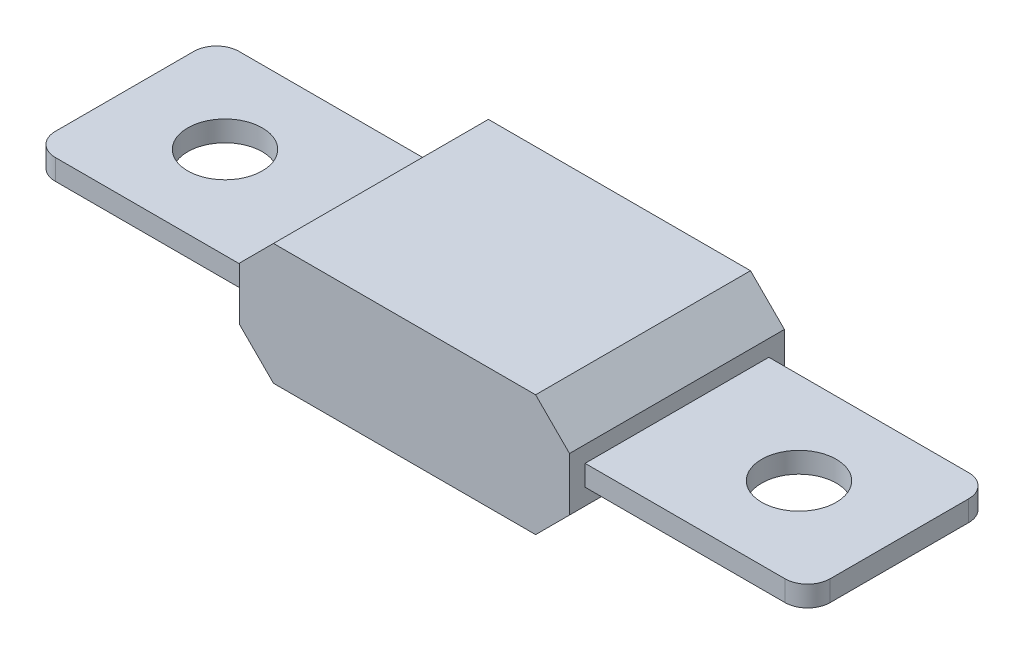
SolidWorks part; units mm, degrees
ref_plane "Front Plane" through (0, 0, 0) normal (0, 0, 1) x (1, 0, 0)
ref_plane "Top Plane" through (0, 0, 0) normal (0, 1, 0) x (1, 0, 0)
ref_plane "Right Plane" through (0, 0, 0) normal (1, 0, 0) x (0, 0, -1)
sketch "Sketch1" plane through (0, 0, 0) normal (0, 1, 0) x (1, 0, 0)
  line L0 (0, -8.13) -> (0, 8.13) construction
  line L1 (-32.29, 8.13) -> (32.29, 8.13)
  line L2 (-34.29, 6.13) -> (-34.29, -6.13)
  line L3 (-32.29, -8.13) -> (32.29, -8.13)
  line L4 (34.29, 6.13) -> (34.29, -6.13)
  line L5 (-34.29, 8.13) -> (34.29, -8.13) construction
  line L6 (-34.29, -8.13) -> (34.29, 8.13) construction
  circle A0 centre (25.4, 0) radius 3.3
  arc A1 (-32.29, 8.13) -> (-34.29, 6.13) centre (-32.29, 6.13) ccw
  arc A2 (-34.29, -6.13) -> (-32.29, -8.13) centre (-32.29, -6.13) ccw
  arc A3 (32.29, 8.13) -> (34.29, 6.13) centre (32.29, 6.13) cw
  arc A4 (32.29, -8.13) -> (34.29, -6.13) centre (32.29, -6.13) ccw
  circle A5 centre (-25.4, 0) radius 3.3
  point P0 (0, 0)
  dimension "D3" = 25.4
  dimension "D4" = 6.6
  dimension "D5" = 2
  dimension "D1" = 68.58
  dimension "D2" = 16.26
extrude "Boss-Extrude1" add sketch "Sketch1" along normal blind 1.83
sketch "Sketch2" plane through (0, 0, 0) normal (0, 0, 1) x (1, 0, 0)
  line L0 (-14.6, 3.275) -> (-11.6, 6.275)
  line L1 (-11.6, 6.275) -> (11.6, 6.275)
  line L2 (-14.6, 3.275) -> (-14.6, -1.445)
  line L3 (-11.6, -4.445) -> (11.6, -4.445)
  line L4 (14.6, 3.275) -> (14.6, -1.445)
  line L5 (-14.6, 6.275) -> (14.6, -4.445) construction
  line L6 (-14.6, -4.445) -> (14.6, 6.275) construction
  line L7 (-14.6, -1.445) -> (-11.6, -4.445)
  line L8 (11.6, 6.275) -> (14.6, 3.275)
  line L9 (11.6, -4.445) -> (14.6, -1.445)
  point P0 (0, 0.915)
  dimension "D1" = 29.2
  dimension "D2" = 0
  dimension "D3" = 10.72
extrude "Boss-Extrude2" add sketch "Sketch2" along normal blind 9.51 and the other way blind 9.51
